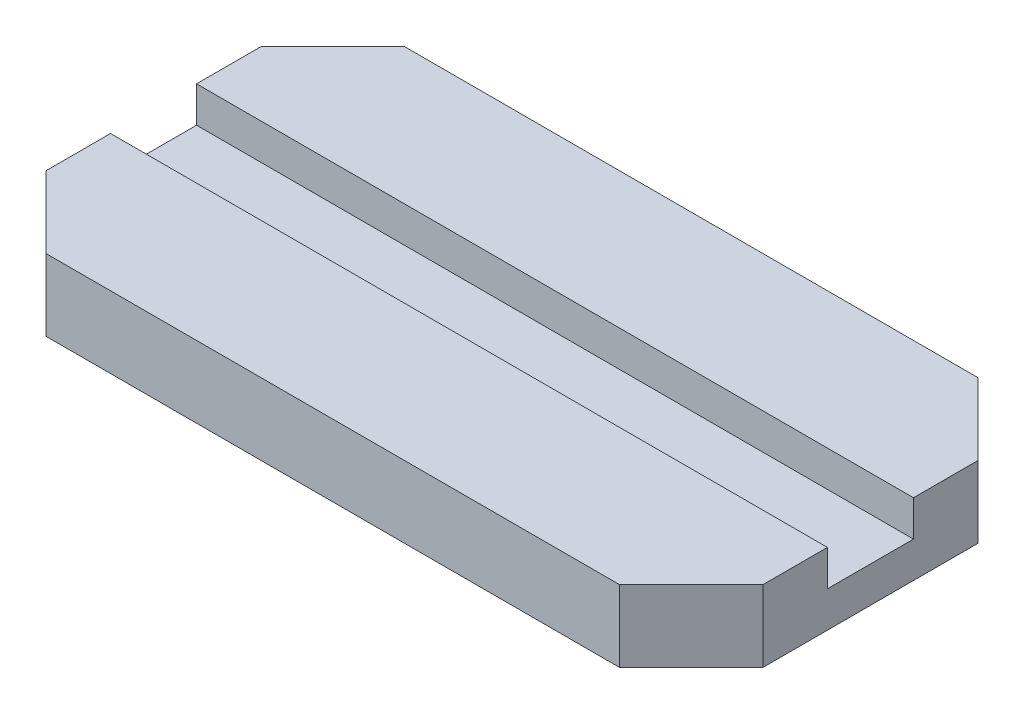
SolidWorks part; units mm, degrees
ref_plane "Front Plane" through (0, 0, 0) normal (0, 0, 1) x (1, 0, 0)
ref_plane "Top Plane" through (0, 0, 0) normal (0, 1, 0) x (1, 0, 0)
ref_plane "Right Plane" through (0, 0, 0) normal (1, 0, 0) x (0, 0, -1)
sketch "Sketch1" plane through (0, 0, 0) normal (0, 1, 0) x (1, 0, 0)
  line L1 (-50, 25) -> (50, 25)
  line L2 (-50, 25) -> (-50, -25)
  line L3 (-50, -25) -> (50, -25)
  line L4 (50, 25) -> (50, -25)
  dimension "D1" = 50
  dimension "D2" = 100
  dimension "D3" = 50
  dimension "D4" = 25
extrude "Boss-Extrude1" add sketch "Sketch1" along normal blind 10
chamfer "Chamfer1" distance 10 angle 45 4 edges at (-50, 5, -25) (-50, 5, 25) (50, 5, -25) (50, 5, 25)
sketch "Sketch2" plane through (0, 10, 0) normal (0, 1, 0) x (1, 0, 0)
  line L1 (-58.3808, 6) -> (54.7849, 6)
  line L2 (-58.3808, 6) -> (-58.3808, -6)
  line L3 (-58.3808, -6) -> (54.7849, -6)
  line L4 (54.7849, 6) -> (54.7849, -6)
  dimension "D1" = 6
  dimension "D2" = 12
extrude "Cut-Extrude1" cut sketch "Sketch2" against normal blind 5
